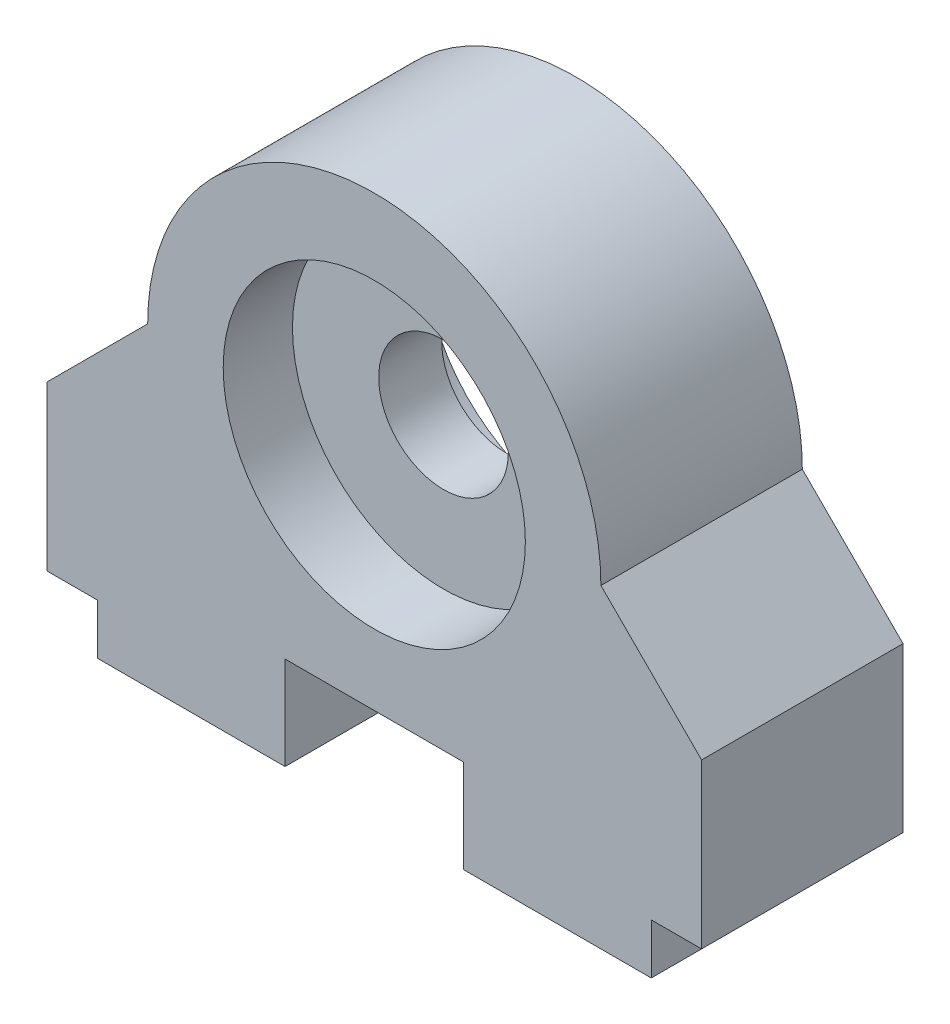
SolidWorks part; units mm, degrees
ref_plane "Front Plane" through (0, 0, 0) normal (0, 0, 1) x (1, 0, 0)
ref_plane "Top Plane" through (0, 0, 0) normal (0, 1, 0) x (1, 0, 0)
ref_plane "Right Plane" through (0, 0, 0) normal (1, 0, 0) x (0, 0, -1)
sketch "Sketch1" plane through (0, 0, 0) normal (0, 0, 1) x (1, 0, 0)
  line L0 (0, -26.1041) -> (0, 52.7781) construction
  line L1 (4.5, 4.699) -> (-4.5, 4.699)
  line L2 (-4.5, 4.699) -> (-4.5, 0)
  line L3 (-4.5, 0) -> (-13.97, 0)
  line L4 (16.51, 2.54) -> (16.51, 10.795)
  line L5 (16.51, 10.795) -> (11.43, 15.875)
  line L6 (4.5, 4.699) -> (4.5, 0)
  line L7 (-16.51, 2.54) -> (-16.51, 10.795)
  line L8 (4.5, 0) -> (13.97, 0)
  line L9 (-16.51, 10.795) -> (-11.43, 15.875)
  line L10 (16.51, 2.54) -> (13.97, 2.54)
  line L11 (13.97, 0) -> (13.97, 2.54)
  line L13 (-16.51, 2.54) -> (-13.97, 2.54)
  line L14 (-13.97, 0) -> (-13.97, 2.54)
  circle A0 centre (0, 15.875) radius 7.62
  arc A1 (-11.43, 15.875) -> (11.43, 15.875) centre (0, 15.875) cw
  point P11 (0, 4.699)
  point P12 (0, 28.448)
  point P15 (0, 8.255)
  dimension "D6" = 15.24
  dimension "D3" = 3.81
  dimension "D1" = 9
  dimension "D2" = 4.699
  dimension "D4" = 45
  dimension "D5" = 15.875
  dimension "D7" = 33.02
  dimension "D8" = 2.54
  dimension "D9" = 2.54
extrude "Boss-Extrude1" add sketch "Sketch1" along normal blind 10.16
ref_plane "Plane1" through (0, 0, 5.08) normal (0, 0, 1) x (1, 0, 0)
sketch "Sketch3" plane through (0, 0, 5.08) normal (0, 0, 1) x (1, 0, 0)
  circle A0 centre (0, 15.875) radius 3.2703
  circle A1 centre (0, 15.875) radius 8.7376
  dimension "D1" = 6.5405
  dimension "D2" = 17.4752
extrude "Boss-Extrude2" add sketch "Sketch3" along normal blind 1.5875 and the other way blind 1.5875
sketch "Sketch4" plane through (0, 0, 0) normal (0, -1, 0) x (-1, 0, 0)
  line L0 (-4.5, 0) -> (-13.97, 0) construction
  line L3 (0, 9.7586) -> (0, -18.8259) construction
  circle A0 centre (-10.16, -3.81) radius 1.9837
  circle A1 centre (10.16, -3.81) radius 1.9837
  dimension "D1" = 3.9675
  dimension "D2" = 10.16
  dimension "D3" = 3.81
extrude "Cut-Extrude1" cut sketch "Sketch4" against normal blind 10.16
equation "\"0.095inin\"=0.085"
